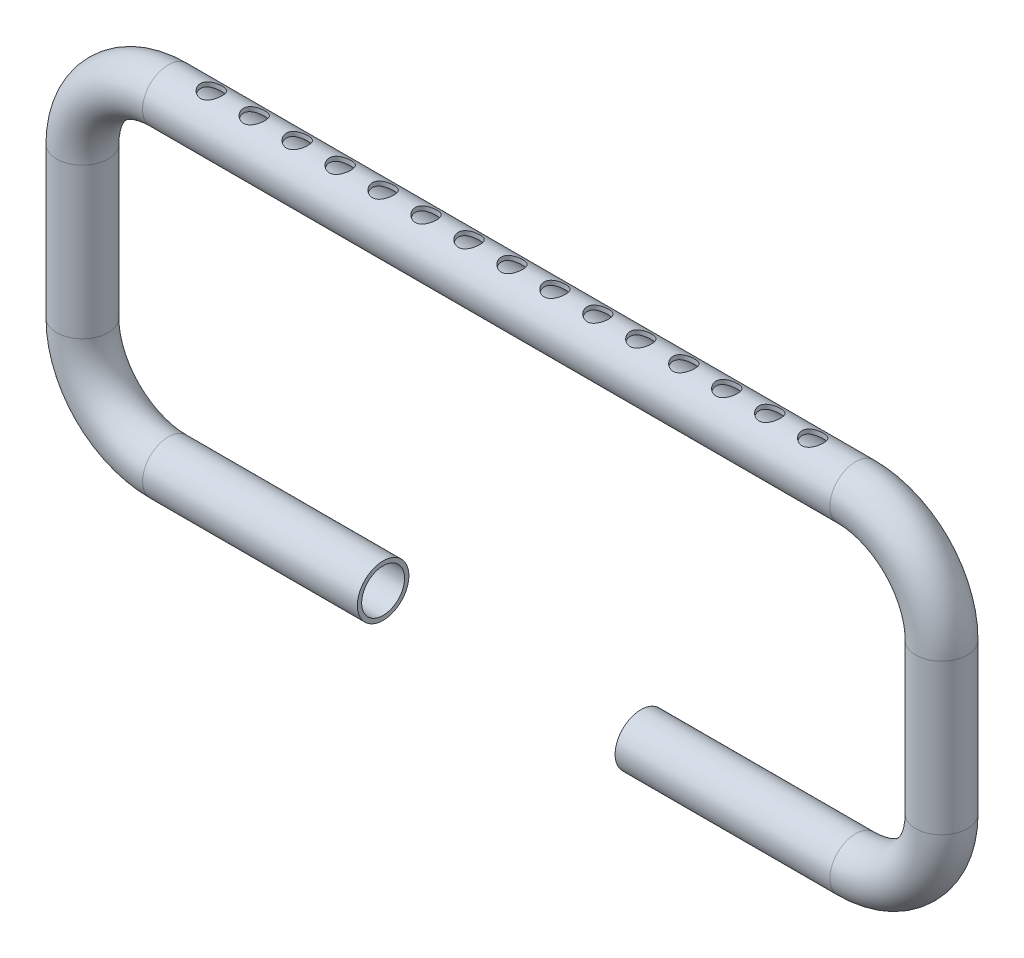
SolidWorks part; units mm, degrees
material "ABS"
ref_plane "Front Plane" through (0, 0, 0) normal (0, 0, 1) x (1, 0, 0)
ref_plane "Top Plane" through (0, 0, 0) normal (0, 1, 0) x (1, 0, 0)
ref_plane "Right Plane" through (0, 0, 0) normal (1, 0, 0) x (0, 0, -1)
sketch "Sketch1" plane through (0, 0, 0) normal (0, 0, 1) x (1, 0, 0)
  line L1 (0, 0) -> (50, 0)
  line L2 (70, 20) -> (70, 55)
  line L3 (50, 75) -> (-110, 75)
  line L4 (-130, 55) -> (-130, 20)
  line L5 (-110, 0) -> (-60, 0)
  arc A0 (-110, 75) -> (-130, 55) centre (-110, 55) ccw
  arc A1 (-130, 20) -> (-110, 0) centre (-110, 20) ccw
  arc A2 (70, 55) -> (50, 75) centre (50, 55) ccw
  arc A3 (50, 0) -> (70, 20) centre (50, 20) ccw
  point P2 (-120.2456, 20)
  point P4 (-85, 0)
  point P16 (-110, 0)
  point P23 (0, 0)
  point P24 (-111.1632, 75)
  point P25 (-130, 55.1249)
  point P26 (-110.2248, 75)
  point P27 (-105.3415, 75)
  point P28 (-115.4512, 75)
  point P29 (70, 55)
  point P30 (50, 75)
  point P31 (70, 55)
  point P32 (70, 20)
  point P33 (50, 0)
  dimension "D4" = 20
  dimension "D5" = 20
  dimension "D6" = 20
  dimension "D7" = 20
  dimension "D1" = 200
  dimension "D2" = 75
  dimension "D3" = 60
sketch "Sketch2" plane through (0, 0, 0) normal (1, 0, 0) x (0, 0, -1)
  circle A0 centre (0, 0) radius 6
  circle A1 centre (0, 0) radius 5
  dimension "D1" = 10
  dimension "D2" = 1
sweep "Sweep1" add profiles "Sketch2" path "Sketch1"
ref_plane "Plane1" through (0, 81, 0) normal (0, 1, 0) x (1, 0, 0)
sketch "Sketch4" plane through (0, 81, 0) normal (0, 1, 0) x (1, 0, 0)
  line L2 (-110, 0) -> (-60, 0) construction
  line L3 (-110, 6) -> (-110, -6) construction
  line L4 (50, 6) -> (50, -6) construction
  circle A0 centre (-100, 0) radius 2.5
  circle A1 centre (-90, 0) radius 2.5
  circle A2 centre (-80, 0) radius 2.5
  circle A3 centre (-70, 0) radius 2.5
  circle A4 centre (-60, 0) radius 2.5
  circle A5 centre (-50, 0) radius 2.5
  circle A6 centre (-40, 0) radius 2.5
  circle A7 centre (-30, 0) radius 2.5
  circle A8 centre (-20, 0) radius 2.5
  circle A9 centre (-10, 0) radius 2.5
  circle A10 centre (0, 0) radius 2.5
  circle A11 centre (10, 0) radius 2.5
  circle A12 centre (20, 0) radius 2.5
  circle A13 centre (30, 0) radius 2.5
  circle A14 centre (40, 0) radius 2.5
  point P2 (0, 0)
  dimension "D1" = 5
  dimension "D3" = 10
  dimension "D4" = 10
  dimension "D2" = 15
extrude "Cut-Extrude1" cut sketch "Sketch4" against normal blind 20
